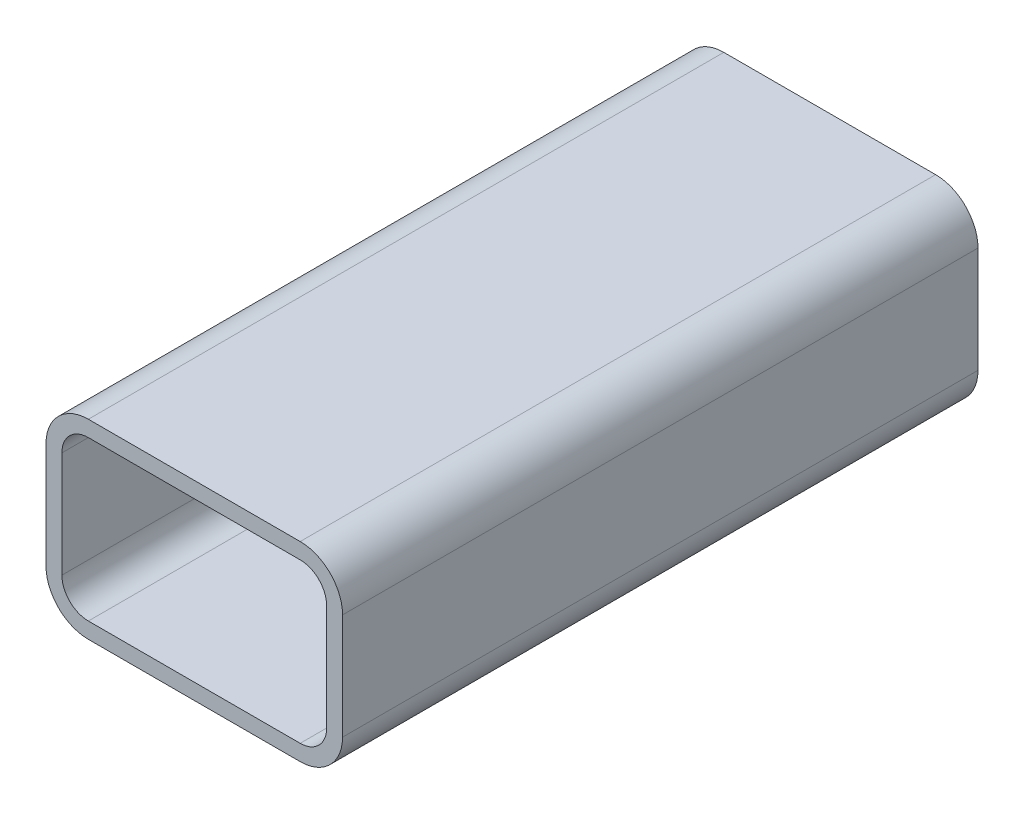
SolidWorks part; units mm, degrees
ref_plane "Front Plane" through (0, 0, 0) normal (0, 0, 1) x (1, 0, 0)
ref_plane "Top Plane" through (0, 0, 0) normal (0, 1, 0) x (1, 0, 0)
ref_plane "Right Plane" through (0, 0, 0) normal (1, 0, 0) x (0, 0, -1)
sketch "Sketch1" plane through (0, 0, 0) normal (0, 0, 1) x (1, 0, 0)
  line L1 (-20, 15) -> (20, 15)
  line L2 (-25, 10) -> (-25, -10)
  line L3 (-20, -15) -> (20, -15)
  line L4 (25, 10) -> (25, -10)
  line L5 (-25, 15) -> (25, -15) construction
  line L6 (-25, -15) -> (25, 15) construction
  arc A0 (20, 15) -> (25, 10) centre (20, 10) cw
  arc A1 (25, -10) -> (20, -15) centre (20, -10) cw
  arc A2 (-20, -15) -> (-25, -10) centre (-20, -10) cw
  arc A3 (-25, 10) -> (-20, 15) centre (-20, 10) cw
  point P0 (0, 0)
  dimension "D3" = 5
  dimension "D1" = 50
  dimension "D2" = 30
extrude "Extrude-Thin1" add sketch "Sketch1" along normal mid plane 120 thin thin type one direction wall 3
sketch "Sketch2" plane through (0, 18, 0) normal (0, 1, 0) x (1, 0, 0)
  line L0 (0, -45) -> (0, 45) construction
  line L1 (-6, -45) -> (-6, 45)
  line L2 (6, -45) -> (6, 45)
  arc A0 (-6, -45) -> (6, -45) centre (0, -45) ccw
  arc A1 (6, 45) -> (-6, 45) centre (0, 45) ccw
  point P2 (0, 0)
  dimension "D2" = 6
  dimension "D1" = 90
extrude "Cut-Extrude1" [suppressed] cut sketch "Sketch2" against normal through all
